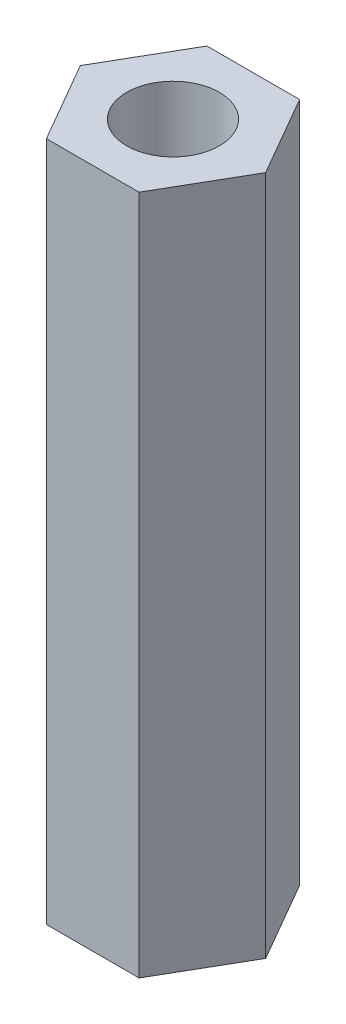
SolidWorks part; units mm, degrees
ref_plane "Front Plane" through (0, 0, 0) normal (0, 0, 1) x (1, 0, 0)
ref_plane "Top Plane" through (0, 0, 0) normal (0, 1, 0) x (1, 0, 0)
ref_plane "Right Plane" through (0, 0, 0) normal (1, 0, 0) x (0, 0, -1)
sketch "Sketch1" plane through (0, 0, 0) normal (0, 1, 0) x (1, 0, 0)
  line L1 (2.996, 0) -> (1.498, 2.5946)
  line L2 (1.498, 2.5946) -> (-1.498, 2.5946)
  line L3 (-1.498, 2.5946) -> (-2.996, 0)
  line L4 (-2.996, 0) -> (-1.498, -2.5946)
  line L5 (-1.498, -2.5946) -> (1.498, -2.5946)
  line L6 (1.498, -2.5946) -> (2.996, 0)
  circle A0 centre (0, 0) radius 1.5
  circle A1 centre (0, 0) radius 2.5946 construction
extrude "Boss-Extrude1" add sketch "Sketch1" along normal blind 22
